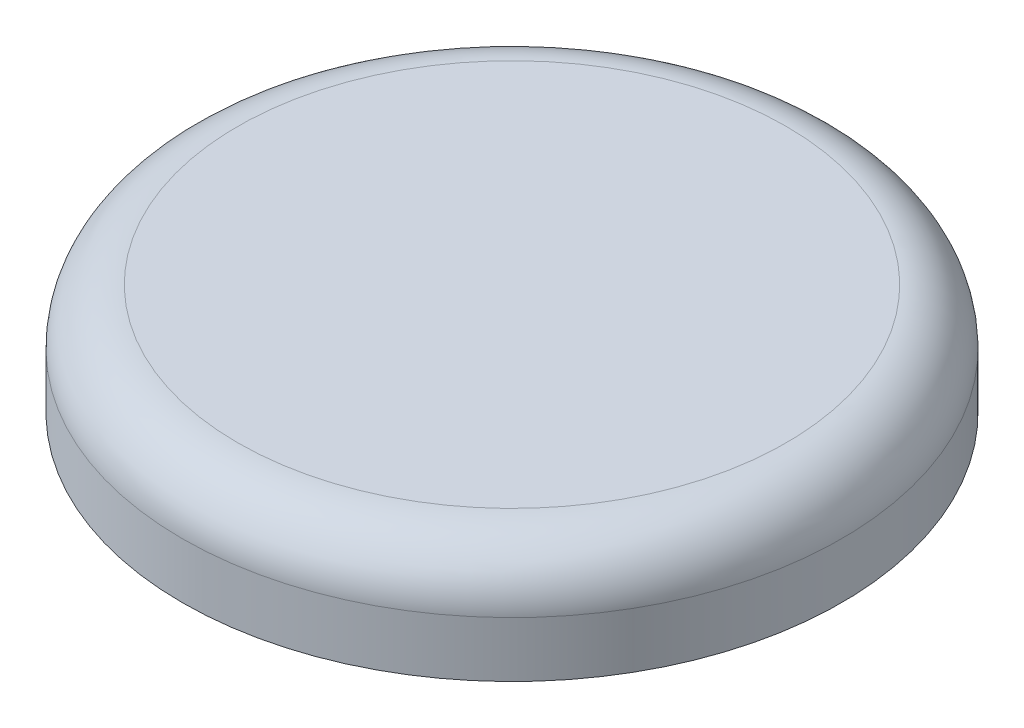
SolidWorks part; units mm, degrees
ref_plane "Front Plane" through (0, 0, 0) normal (0, 0, 1) x (1, 0, 0)
ref_plane "Top Plane" through (0, 0, 0) normal (0, 1, 0) x (1, 0, 0)
ref_plane "Right Plane" through (0, 0, 0) normal (1, 0, 0) x (0, 0, -1)
sketch "Sketch1" plane through (0, 0, 0) normal (0, 1, 0) x (1, 0, 0)
  circle A0 centre (0, 0) radius 5.95
extrude "Boss-Extrude1" add sketch "Sketch1" along normal blind 2 contours A0
fillet "Fillet1" radius 1 1 edges at (0, 2, 5.95)
